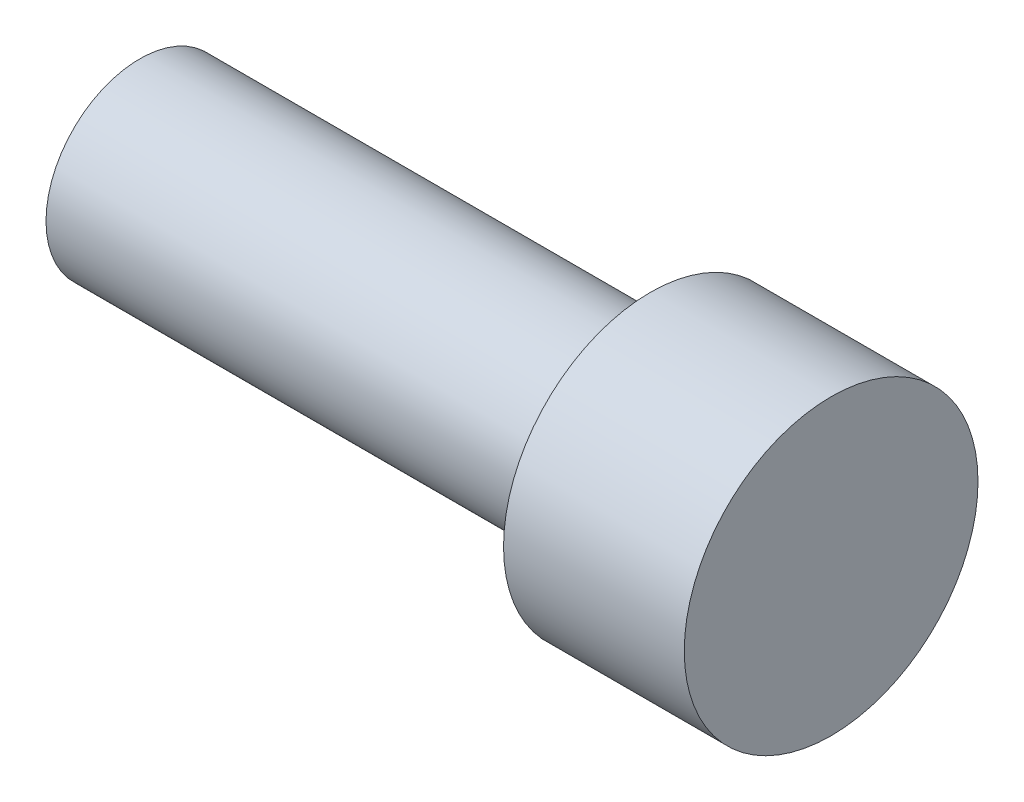
SolidWorks part; units mm, degrees
ref_plane "Front Plane" through (0, 0, 0) normal (0, 0, 1) x (1, 0, 0)
ref_plane "Top Plane" through (0, 0, 0) normal (0, 1, 0) x (1, 0, 0)
ref_plane "Right Plane" through (0, 0, 0) normal (1, 0, 0) x (0, 0, -1)
sketch "Sketch1" plane through (0, 0, 0) normal (1, 0, 0) x (0, 0, -1)
  circle A0 centre (0, 0) radius 2.075
  dimension "D1" = 4.15
extrude "Boss-Extrude1" add sketch "Sketch1" along normal blind 11.3
sketch "Sketch2" plane through (11.3, 0, 0) normal (1, 0, 0) x (0, 0, -1)
  circle A0 centre (0, 0) radius 3.25
  dimension "D1" = 6.5
extrude "Boss-Extrude2" add sketch "Sketch2" along normal blind 4
